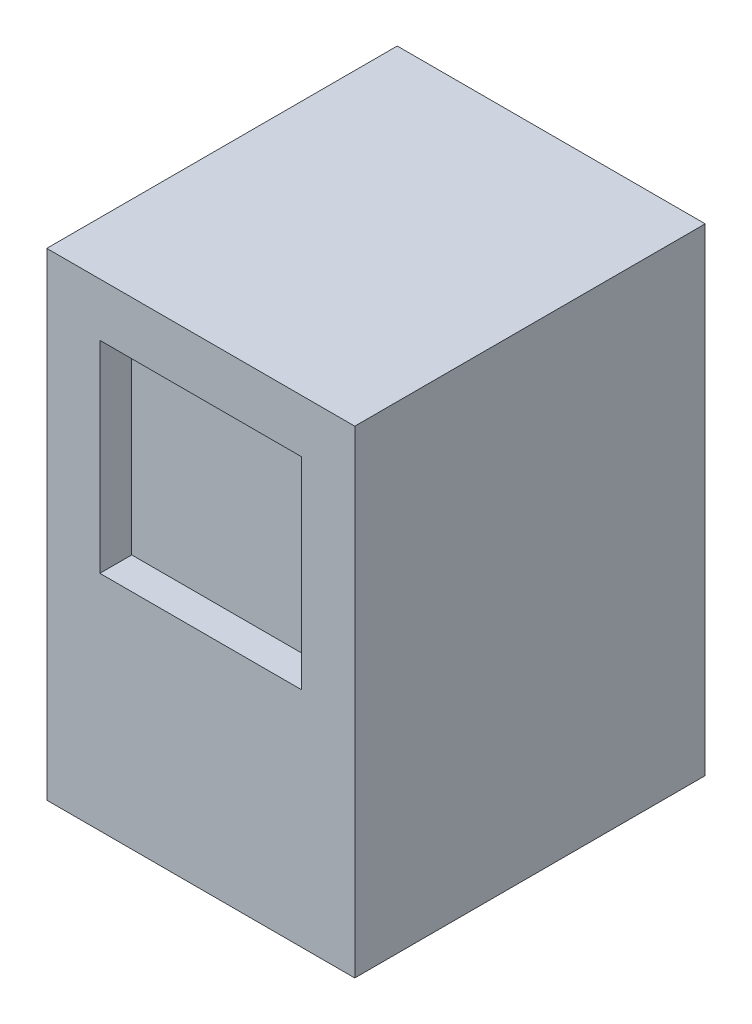
SolidWorks part; units mm, degrees
ref_plane "Front Plane" through (0, 0, 0) normal (0, 0, 1) x (1, 0, 0)
ref_plane "Top Plane" through (0, 0, 0) normal (0, 1, 0) x (1, 0, 0)
ref_plane "Right Plane" through (0, 0, 0) normal (1, 0, 0) x (0, 0, -1)
sketch "Sketch1" plane through (0, 0, 0) normal (0, 1, 0) x (1, 0, 0)
  line L1 (-368.3, -419.1) -> (368.3, -419.1)
  line L2 (-368.3, -419.1) -> (-368.3, 419.1)
  line L3 (-368.3, 419.1) -> (368.3, 419.1)
  line L4 (368.3, -419.1) -> (368.3, 419.1)
  line L5 (-368.3, -419.1) -> (368.3, 419.1) construction
  line L6 (-368.3, 419.1) -> (368.3, -419.1) construction
  point P0 (0, 0)
  dimension "D1" = 736.6
  dimension "D2" = 838.2
extrude "Boss-Extrude1" add sketch "Sketch1" along normal blind 1143
sketch "Sketch3" plane through (0, 0, 419.1) normal (0, 0, 1) x (1, 0, 0)
  line L0 (-368.3, 1143) -> (-368.3, 0) construction
  line L1 (-241.3, 533.4) -> (241.3, 533.4)
  line L2 (-241.3, 533.4) -> (-241.3, 1016)
  line L3 (-241.3, 1016) -> (241.3, 1016)
  line L4 (241.3, 533.4) -> (241.3, 1016)
  line L5 (-241.3, 533.4) -> (241.3, 1016) construction
  line L6 (-241.3, 1016) -> (241.3, 533.4) construction
  line L8 (368.3, 1143) -> (368.3, 0) construction
  line L9 (-368.3, 1143) -> (368.3, 1143) construction
  line L10 (-368.3, 0) -> (368.3, 0) construction
  point P0 (0, 774.7)
  dimension "D1" = 127
  dimension "D2" = 127
  dimension "D3" = 127
  dimension "D4" = 533.4
extrude "Cut-Extrude1" cut sketch "Sketch3" against normal blind 76.2
